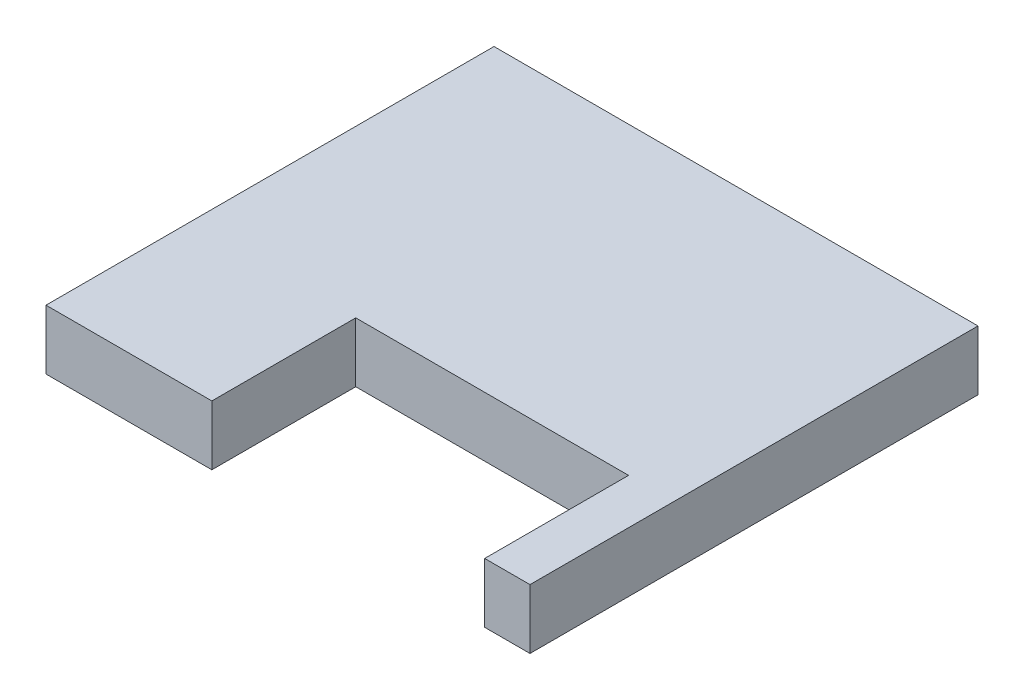
SolidWorks part; units mm, degrees
ref_plane "Front Plane" through (0, 0, 0) normal (0, 0, 1) x (1, 0, 0)
ref_plane "Top Plane" through (0, 0, 0) normal (0, 1, 0) x (1, 0, 0)
ref_plane "Right Plane" through (0, 0, 0) normal (1, 0, 0) x (0, 0, -1)
sketch "Sketch1" plane through (0, 0, 0) normal (0, 1, 0) x (1, 0, 0)
  line L0 (110.3072, 0) -> (110.3072, 102.108)
  line L1 (110.3072, 102.108) -> (0, 102.108)
  line L2 (0, 102.108) -> (0, 0)
  line L3 (0, 0) -> (37.8008, 0)
  line L4 (37.8008, 0) -> (37.8008, 32.794)
  line L5 (37.8008, 32.794) -> (99.9808, 32.794)
  line L6 (99.9808, 32.794) -> (99.9808, 0)
  line L7 (99.9808, 0) -> (110.3072, 0)
  line L10 (55.1536, 101.854) -> (55.1536, 102.108) construction
  dimension "D1" = 110.3072
  dimension "D2" = 10.3264
  dimension "D3" = 102.108
  dimension "D4" = 37.8008
  dimension "D5" = 32.794
extrude "Boss-Extrude1" add sketch "Sketch1" along normal blind 13.5992
